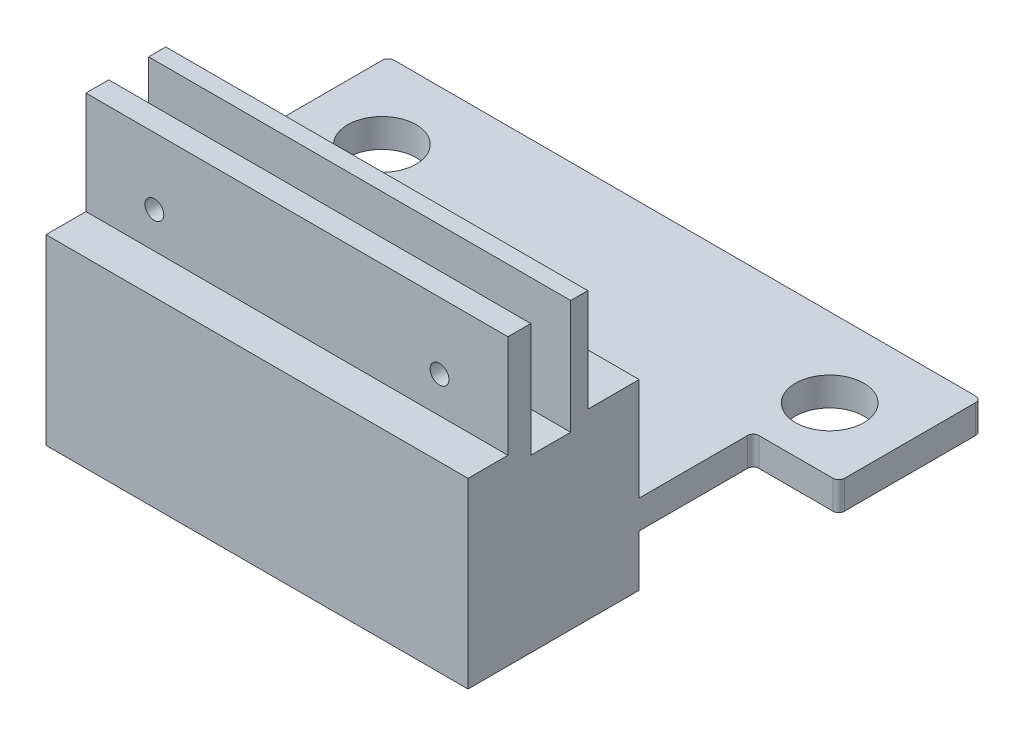
SolidWorks part; units mm, degrees
ref_plane "Front Plane" through (0, 0, 0) normal (0, 0, 1) x (1, 0, 0)
ref_plane "Top Plane" through (0, 0, 0) normal (0, 1, 0) x (1, 0, 0)
ref_plane "Right Plane" through (0, 0, 0) normal (1, 0, 0) x (0, 0, -1)
sketch "Sketch1" plane through (0, 0, 0) normal (0, 0, 1) x (1, 0, 0)
  line L1 (0, 0) -> (74, 0)
  line L2 (0, 0) -> (0, 50)
  line L3 (0, 50) -> (74, 50)
  line L4 (74, 0) -> (74, 50)
  dimension "D1" = 50
  dimension "D2" = 74
extrude "Boss-Extrude1" add sketch "Sketch1" along normal blind 30
sketch "Sketch2" plane through (0, 0, 0) normal (0, -1, 0) x (1, 0, 0)
  line L0 (0, 0) -> (74, 0) construction
  line L1 (0, 30) -> (0, 0) construction
  circle A0 centre (12.74, 15) radius 10.5
  circle A1 centre (61.2617, 15) radius 10.5
  dimension "D1" = 21
  dimension "D2" = 21
  dimension "D3" = 15
  dimension "D4" = 15
  dimension "D5" = 48.5217
  dimension "D6" = 12.74
extrude "Cut-Extrude1" cut sketch "Sketch2" against normal blind 10
sketch "Sketch3" plane through (0, 10, 0) normal (0, -1, 0) x (1, 0, 0)
  circle A0 centre (12.74, 15) radius 6.25
  circle A1 centre (61.2617, 15) radius 6.25
  dimension "D1" = 12.5
  dimension "D2" = 12.5
extrude "Cut-Extrude2" cut sketch "Sketch3" against normal blind 10
sketch "Sketch4" plane through (0, 0, 0) normal (-1, 0, 0) x (0, 0, 1)
  line L0 (30, 50) -> (0, 50) construction
  line L1 (12, 50) -> (19, 50)
  line L2 (12, 50) -> (12, 30)
  line L3 (12, 30) -> (19, 30)
  line L4 (19, 50) -> (19, 30)
  line L5 (30, 50) -> (30, 0) construction
  dimension "D1" = 7
  dimension "D2" = 11
  dimension "D3" = 20
extrude "Cut-Extrude3" cut sketch "Sketch4" against normal blind 111
sketch "Sketch5" plane through (74, 0, 0) normal (1, 0, 0) x (0, 0, -1)
  line L0 (-19, 30) -> (-19, 50) construction
  line L1 (-30, 50) -> (-23, 50)
  line L2 (-30, 50) -> (-30, 32)
  line L3 (-30, 32) -> (-23, 32)
  line L4 (-23, 50) -> (-23, 32)
  line L5 (0, 50) -> (-9, 50)
  line L6 (0, 50) -> (0, 32)
  line L7 (0, 32) -> (-9, 32)
  line L8 (-9, 50) -> (-9, 32)
  line L9 (-12, 50) -> (-12, 30) construction
  line L10 (-30, 50) -> (-19, 50) construction
  dimension "D1" = 4
  dimension "D2" = 3
  dimension "D3" = 18
  dimension "D4" = 18
extrude "Cut-Extrude4" cut sketch "Sketch5" against normal blind 111
sketch "Sketch6" plane through (0, 0, 9) normal (0, 0, -1) x (-1, 0, 0)
  line L0 (-74, 50) -> (-74, 32) construction
  circle A0 centre (-62, 38.3089) radius 1.65
  circle A1 centre (-12, 38.3089) radius 1.65
  dimension "D1" = 3.3
  dimension "D2" = 3.3
  dimension "D3" = 50
  dimension "D4" = 12
extrude "Cut-Extrude5" cut sketch "Sketch6" against normal blind 111
sketch "Sketch7" plane through (0, 0, 0) normal (0, 0, -1) x (-1, 0, 0)
  line L0 (0, 32) -> (0, 0) construction
  line L1 (-74, 9) -> (0, 9)
  line L2 (-74, 9) -> (-74, 14)
  line L3 (-74, 14) -> (0, 14)
  line L4 (0, 9) -> (0, 14)
  line L5 (0, 0) -> (-74, 0) construction
  dimension "D1" = 5
  dimension "D2" = 9
extrude "Boss-Extrude2" add sketch "Sketch7" along normal blind 45
sketch "Sketch8" plane through (74, 0, 0) normal (1, 0, 0) x (0, 0, -1)
  line L1 (45, 14) -> (20, 14)
  line L2 (45, 14) -> (45, 9)
  line L3 (45, 9) -> (20, 9)
  line L4 (20, 14) -> (20, 9)
  dimension "D1" = 25
  dimension "D2" = 5
extrude "Boss-Extrude3" add sketch "Sketch8" along normal blind 15
sketch "Sketch9" plane through (0, 0, 0) normal (-1, 0, 0) x (0, 0, 1)
  line L1 (-45, 14) -> (-20, 14)
  line L2 (-45, 14) -> (-45, 9)
  line L3 (-45, 9) -> (-20, 9)
  line L4 (-20, 14) -> (-20, 9)
  dimension "D1" = 25
  dimension "D2" = 5
extrude "Boss-Extrude4" add sketch "Sketch9" along normal blind 15
sketch "Sketch10" plane through (0, 0, 0) normal (0, -1, 0) x (1, 0, 0)
  circle A0 centre (-2.254, -31.1469) radius 6
  circle A1 centre (76.2557, -31.1469) radius 6
  dimension "D1" = 12
  dimension "D2" = 12
extrude "Cut-Extrude6" cut sketch "Sketch10" against normal blind 50
fillet "Fillet1" radius 1 6 edges at (74, 11.5, -20) (89, 11.5, -20) (89, 11.5, -45) (-15, 11.5, -45) (0, 11.5, -20) (-15, 11.5, -20)
